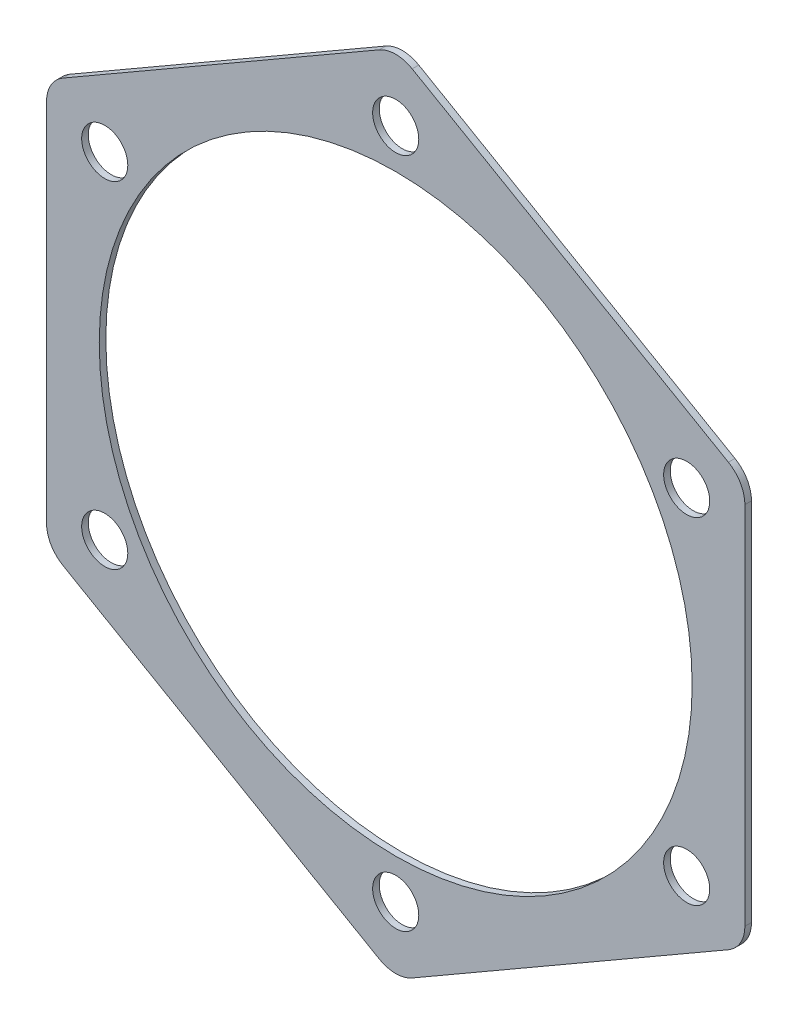
SolidWorks part; units mm, degrees
ref_plane "Front Plane" through (0, 0, 0) normal (0, 0, 1) x (1, 0, 0)
ref_plane "Top Plane" through (0, 0, 0) normal (0, 1, 0) x (1, 0, 0)
ref_plane "Right Plane" through (0, 0, 0) normal (1, 0, 0) x (0, 0, -1)
sketch "Sketch1" plane through (0, 0, 0) normal (0, 0, 1) x (1, 0, 0)
  line L1 (-50.5, -32.0429) -> (-2.5, -59.7558)
  line L2 (2.5, -59.7558) -> (50.5, -32.0429)
  line L3 (53, -27.7128) -> (53, 27.7128)
  line L4 (50.5, 32.0429) -> (2.5, 59.7558)
  line L5 (-2.5, 59.7558) -> (-50.5, 32.0429)
  line L6 (-53, 27.7128) -> (-53, -27.7128)
  circle A0 centre (0, 0) radius 53 construction
  circle A1 centre (0, 0) radius 51 construction
  circle A2 centre (0, 0) radius 45
  arc A3 (-50.5, -32.0429) -> (-53, -27.7128) centre (-48, -27.7128) cw
  arc A4 (-2.5, -59.7558) -> (2.5, -59.7558) centre (0, -55.4256) ccw
  arc A5 (50.5, -32.0429) -> (53, -27.7128) centre (48, -27.7128) ccw
  arc A6 (53, 27.7128) -> (50.5, 32.0429) centre (48, 27.7128) ccw
  arc A7 (2.5, 59.7558) -> (-2.5, 59.7558) centre (0, 55.4256) ccw
  arc A8 (-50.5, 32.0429) -> (-53, 27.7128) centre (-48, 27.7128) ccw
  circle A9 centre (0, 51) radius 3.5
  circle A10 centre (44.1673, 25.5) radius 3.5
  circle A11 centre (44.1673, -25.5) radius 3.5
  circle A12 centre (0, -51) radius 3.5
  circle A13 centre (-44.1673, -25.5) radius 3.5
  circle A14 centre (-44.1673, 25.5) radius 3.5
  point P37 (0, 0)
  dimension "D2" = 102
  dimension "D3" = 90
  dimension "D4" = 5
  dimension "D5" = 7
  dimension "D1" = 106
  dimension "D6" = 6
extrude "Boss-Extrude1" add sketch "Sketch1" along normal blind 1
